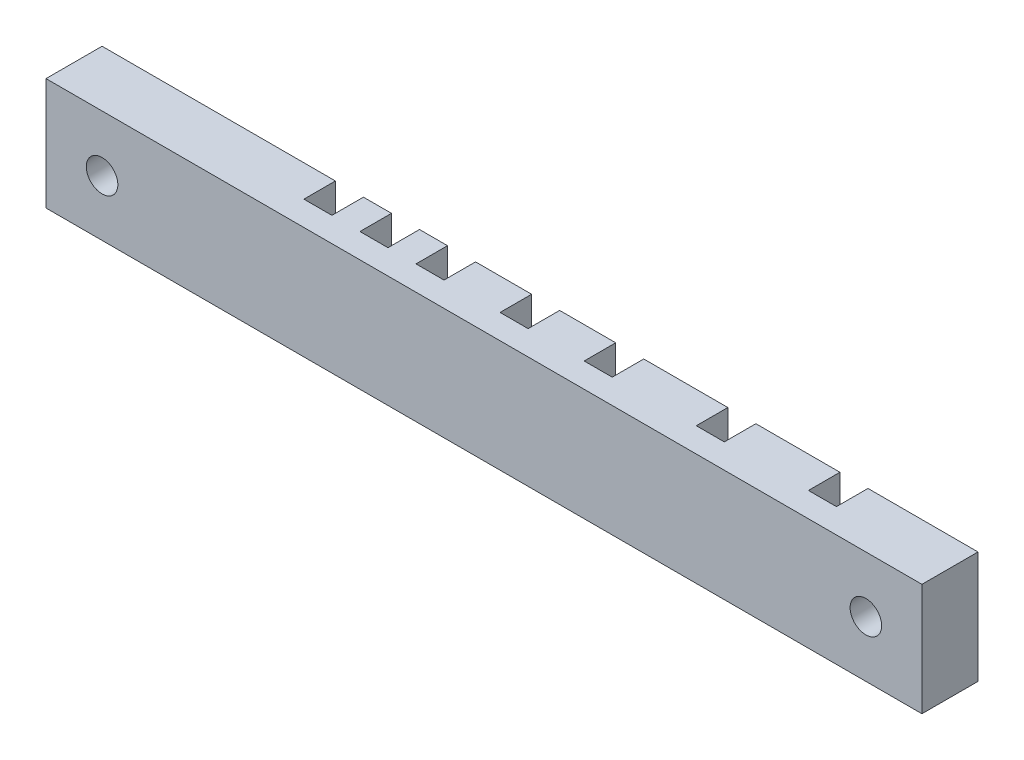
SolidWorks part; units mm, degrees
ref_plane "Front Plane" through (0, 0, 0) normal (0, 0, 1) x (1, 0, 0)
ref_plane "Top Plane" through (0, 0, 0) normal (0, 1, 0) x (1, 0, 0)
ref_plane "Right Plane" through (0, 0, 0) normal (1, 0, 0) x (0, 0, -1)
sketch "Sketch2" plane through (0, 0, 0) normal (0, 0, 1) x (1, 0, 0)
  line L1 (-58.7929, 14.243) -> (66.2071, 14.243)
  line L2 (-58.7929, 14.243) -> (-58.7929, -1.757)
  line L3 (-58.7929, -1.757) -> (66.2071, -1.757)
  line L4 (66.2071, 14.243) -> (66.2071, -1.757)
  dimension "D1" = 125
  dimension "D2" = 16
extrude "Boss-Extrude1" add sketch "Sketch2" along normal blind 8
sketch "Sketch3" plane through (0, 14.243, 0) normal (0, 1, 0) x (1, 0, 0)
  line L0 (66.2071, -8) -> (66.2071, 0) construction
  line L1 (50.5071, -4.5) -> (46.5071, -4.5)
  line L2 (50.5071, -4.5) -> (50.5071, 2.3636)
  line L3 (50.5071, 2.3636) -> (46.5071, 2.3636)
  line L4 (46.5071, -4.5) -> (46.5071, 2.3636)
  line L5 (66.2071, 0) -> (-58.7929, 0) construction
  line L7 (34.5071, -4.5) -> (30.5071, -4.5)
  line L8 (34.5071, -4.5) -> (34.5071, 5.9193)
  line L9 (34.5071, 5.9193) -> (30.5071, 5.9193)
  line L10 (30.5071, -4.5) -> (30.5071, 5.9193)
  line L11 (18.5071, -4.5) -> (14.5071, -4.5)
  line L12 (18.5071, -4.5) -> (18.5071, 5.9193)
  line L13 (18.5071, 5.9193) -> (14.5071, 5.9193)
  line L14 (14.5071, -4.5) -> (14.5071, 5.9193)
  line L19 (6.5071, -4.5) -> (2.5071, -4.5)
  line L20 (6.5071, -4.5) -> (6.5071, 5.9193)
  line L21 (6.5071, 5.9193) -> (2.5071, 5.9193)
  line L22 (2.5071, -4.5) -> (2.5071, 5.9193)
  line L23 (-5.4929, -4.5) -> (-9.4929, -4.5)
  line L24 (-5.4929, -4.5) -> (-5.4929, 5.9193)
  line L25 (-5.4929, 5.9193) -> (-9.4929, 5.9193)
  line L26 (-9.4929, -4.5) -> (-9.4929, 5.9193)
  line L27 (-13.4929, -4.5) -> (-17.4929, -4.5)
  line L28 (-13.4929, -4.5) -> (-13.4929, 5.9193)
  line L29 (-13.4929, 5.9193) -> (-17.4929, 5.9193)
  line L30 (-17.4929, -4.5) -> (-17.4929, 5.9193)
  line L31 (-21.4929, -4.5) -> (-25.4929, -4.5)
  line L32 (-21.4929, -4.5) -> (-21.4929, 5.9193)
  line L33 (-21.4929, 5.9193) -> (-25.4929, 5.9193)
  line L34 (-25.4929, -4.5) -> (-25.4929, 5.9193)
  dimension "D1" = 15.7
  dimension "D2" = 4
  dimension "D3" = 4.5
  dimension "D4" = 31.7
  dimension "D5" = 4
  dimension "D6" = 47.7
  dimension "D7" = 4
  dimension "D8" = 4
  dimension "D9" = 59.7
  dimension "D10" = 71.7
  dimension "D11" = 79.7
  dimension "D12" = 87.7
extrude "Cut-Extrude1" cut sketch "Sketch3" against normal through all
sketch "Sketch4" plane through (0, 0, 0) normal (0, 0, -1) x (-1, 0, 0)
  line L0 (58.7929, 14.243) -> (58.7929, -1.757) construction
  line L1 (-66.2071, -1.757) -> (-66.2071, 14.243) construction
  circle A0 centre (50.7929, 6.243) radius 4
  circle A1 centre (-58.2071, 6.243) radius 4
  dimension "D1" = 8
  dimension "D3" = 8
  dimension "D2" = 8
extrude "Cut-Extrude2" cut sketch "Sketch4" against normal blind 4.4
sketch "Sketch5" plane through (0, 0, 4.4) normal (0, 0, -1) x (-1, 0, 0)
  circle A0 centre (50.7929, 6.243) radius 2.25
  circle A1 centre (-58.2071, 6.243) radius 2.25
  dimension "D1" = 4.5
extrude "Cut-Extrude3" cut sketch "Sketch5" against normal through all
